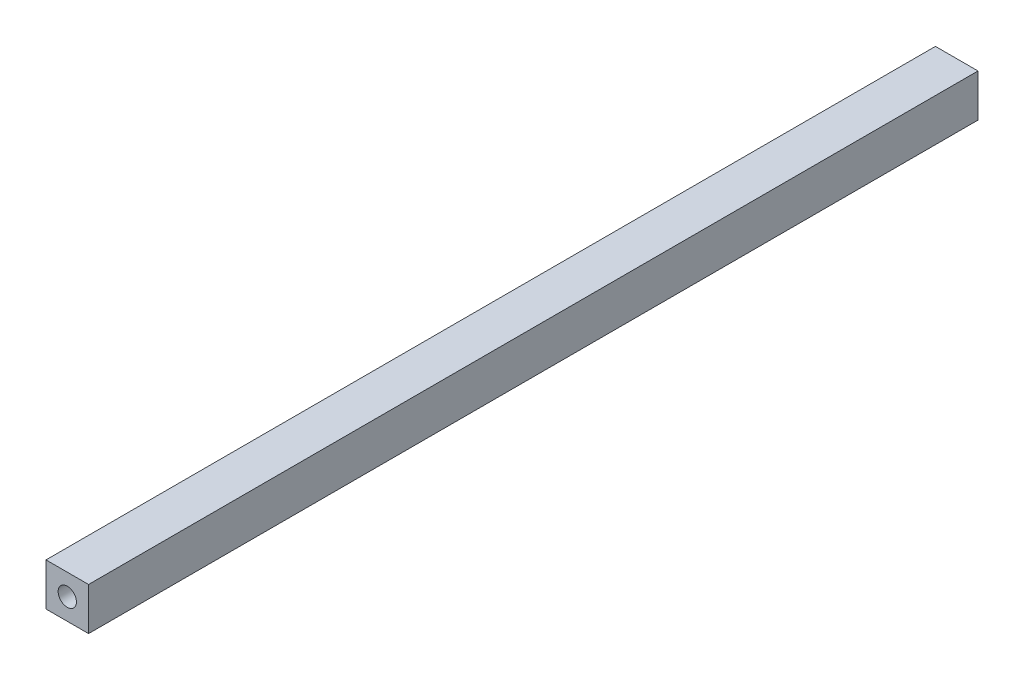
SolidWorks part; units mm, degrees
ref_plane "Ön Düzlem" through (0, 0, 0) normal (0, 0, 1) x (1, 0, 0)
ref_plane "Üst Düzlem" through (0, 0, 0) normal (0, 1, 0) x (1, 0, 0)
ref_plane "Sağ Düzlem" through (0, 0, 0) normal (1, 0, 0) x (0, 0, -1)
sketch "Çizim1" plane through (0, 0, 0) normal (0, 0, 1) x (1, 0, 0)
  line L1 (-14, -14) -> (14, -14)
  line L2 (-14, -14) -> (-14, 14)
  line L3 (-14, 14) -> (14, 14)
  line L4 (14, -14) -> (14, 14)
  line L5 (-14, -14) -> (14, 14) construction
  line L6 (-14, 14) -> (14, -14) construction
  point P0 (0, 0)
  dimension "D1" = 28
  dimension "D2" = 28
extrude "Yükseklik-Ekstrüzyon1" add sketch "Çizim1" along normal blind 585
sketch "Çizim2" plane through (0, 0, 585) normal (0, 0, 1) x (1, 0, 0)
  circle A0 centre (0, 0) radius 6
  dimension "D1" = 12
extrude "Kes-Ekstrüzyon1" cut sketch "Çizim2" against normal blind 60
